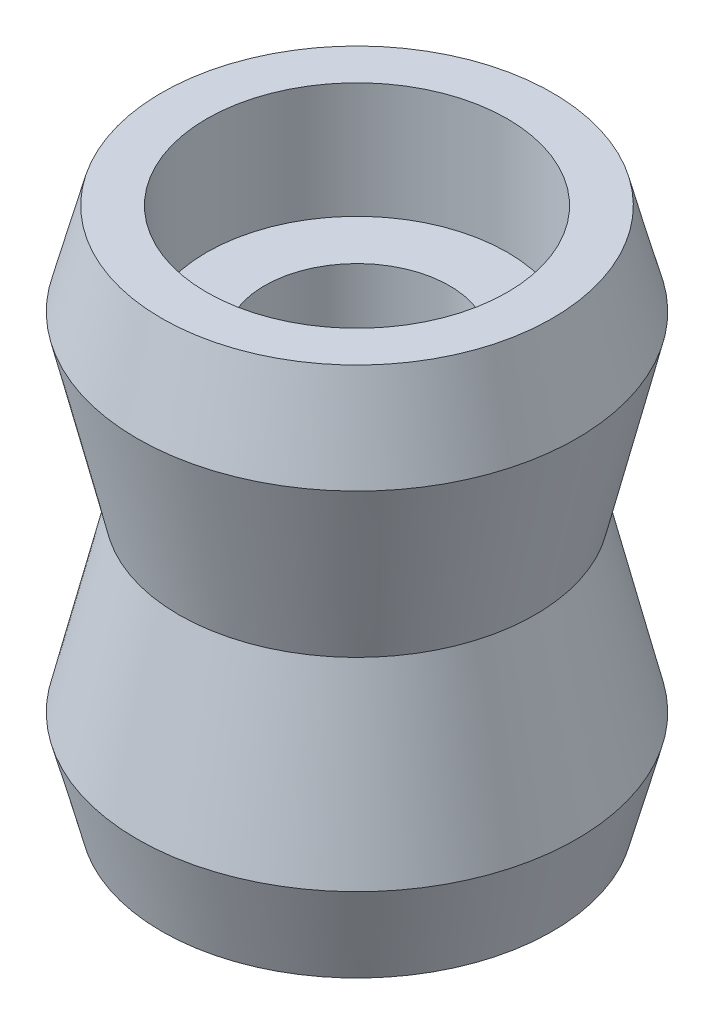
SolidWorks part; units mm, degrees
material "Maple"
ref_plane "Wasteboard" through (0, 0, 0) normal (0, 0, 1) x (1, 0, 0)
ref_plane "Left-Right" through (0, 0, 0) normal (0, 1, 0) x (1, 0, 0)
ref_plane "Front-Back" through (0, 0, 0) normal (1, 0, 0) x (0, 0, -1)
sketch "Sketch1" plane through (0, 0, 0) normal (0, 0, 1) x (1, 0, 0)
  line L0 (0, 42.3235) -> (0, -39.784) construction
  line L1 (0, -55) -> (0, 55) construction
  line L2 (0, 3.1923) -> (40.4814, 3.1923) construction
  line L3 (40.4814, 3.1923) -> (40.4814, 18.1923) construction
  line L4 (30.9163, 3.1923) -> (30.9163, 10.1923) construction
  line L5 (0, 30.7268) -> (2.5, 30.7268) construction
  line L6 (0, 37.5678) -> (4, 37.5678) construction
  line L7 (0, 43.5419) -> (6.5, 43.5419) construction
  line L8 (4, -3.2844) -> (4, 9.669)
  line L9 (4, 9.669) -> (6.5, 9.669)
  line L10 (6.5, 9.669) -> (6.5, 14.669)
  line L11 (6.5, 14.669) -> (8.4483, 14.669)
  line L12 (8.4483, 14.669) -> (9.5, 10.6923)
  line L13 (9.5, 10.6923) -> (7.7, 3.1923)
  line L14 (9.5, -4.3077) -> (7.7, 3.1923)
  line L15 (8.4483, -8.2844) -> (9.5, -4.3077)
  line L16 (6.5, -8.2844) -> (8.4483, -8.2844)
  line L17 (6.5, -3.2844) -> (6.5, -8.2844)
  line L18 (4, -3.2844) -> (6.5, -3.2844)
  line L19 (28.6361, 3.1923) -> (28.6361, 14.6923) construction
  line L20 (28.6361, 14.6923) -> (-15.8373, 14.6923) construction
  line L21 (9.5, 10.6923) -> (7.5155, 18.1962) construction
  point P18 (0, 0)
  point P25 (4, 3.1923)
  point P34 (8.4483, 14.669)
  dimension "D1" = 15
  dimension "D2" = 7
  dimension "D3" = 4
  dimension "D4" = 2.5
  dimension "D5" = 6.5
  dimension "D6" = 5.5
  dimension "D7" = 7.5
  dimension "D9" = 2.5
  dimension "D10" = 82.1075
  dimension "D11" = 5
  dimension "D13" = 11.5
  dimension "D14" = 3.7
revolve "Revolve1" add sketch "Sketch1" angle 360 about L0
